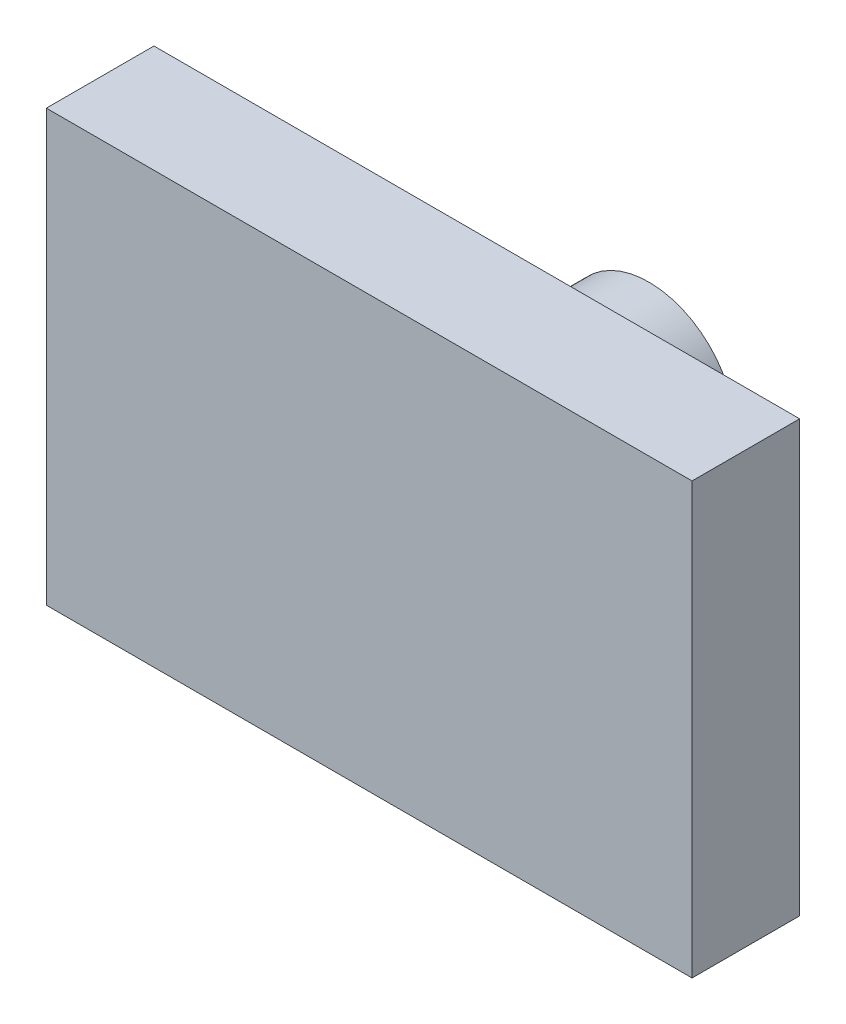
SolidWorks part; units mm, degrees
ref_plane "Alzado" through (0, 0, 0) normal (0, 0, 1) x (1, 0, 0)
ref_plane "Planta" through (0, 0, 0) normal (0, 1, 0) x (1, 0, 0)
ref_plane "Vista lateral" through (0, 0, 0) normal (1, 0, 0) x (0, 0, -1)
sketch "Croquis1" plane through (0, 0, 0) normal (0, 0, 1) x (1, 0, 0)
  line L1 (-15, 10) -> (15, 10)
  line L2 (-15, 10) -> (-15, -10)
  line L3 (-15, -10) -> (15, -10)
  line L4 (15, 10) -> (15, -10)
  line L5 (-15, 10) -> (15, -10) construction
  line L6 (-15, -10) -> (15, 10) construction
  point P0 (0, 0)
  dimension "D1" = 30
  dimension "D2" = 20
extrude "Saliente-Extruir1" add sketch "Croquis1" along normal blind 5 contours L1 L4 L3 L2
sketch "Croquis2" plane through (0, 0, 0) normal (0, 0, -1) x (-1, 0, 0)
  circle A0 centre (0, 0) radius 4
  dimension "D1" = 8
extrude "Saliente-Extruir3" add sketch "Croquis2" along normal blind 8
sketch "Croquis3" plane through (0, 0, -8) normal (0, 0, -1) x (-1, 0, 0)
  circle A0 centre (0, 0) radius 2.1
  dimension "D1" = 4.2
extrude "Cortar-Extruir1" cut sketch "Croquis3" against normal blind 6.5
